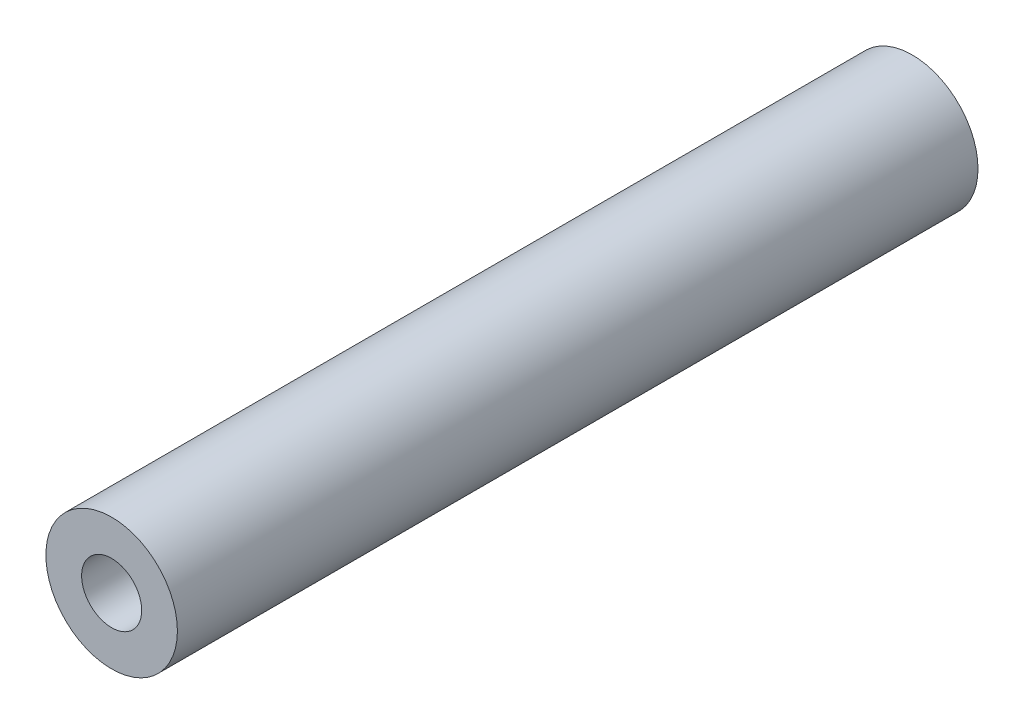
SolidWorks part; units mm, degrees
ref_plane "Front Plane" through (0, 0, 0) normal (0, 0, 1) x (1, 0, 0)
ref_plane "Top Plane" through (0, 0, 0) normal (0, 1, 0) x (1, 0, 0)
ref_plane "Right Plane" through (0, 0, 0) normal (1, 0, 0) x (0, 0, -1)
sketch "Sketch1" plane through (0, 0, 0) normal (0, 0, 1) x (1, 0, 0)
  circle A0 centre (0, 0) radius 2.3
  circle A1 centre (0, 0) radius 1.05
  dimension "D1" = 4.6
  dimension "D2" = 2.1
extrude "Boss-Extrude1" add sketch "Sketch1" along normal blind 28
